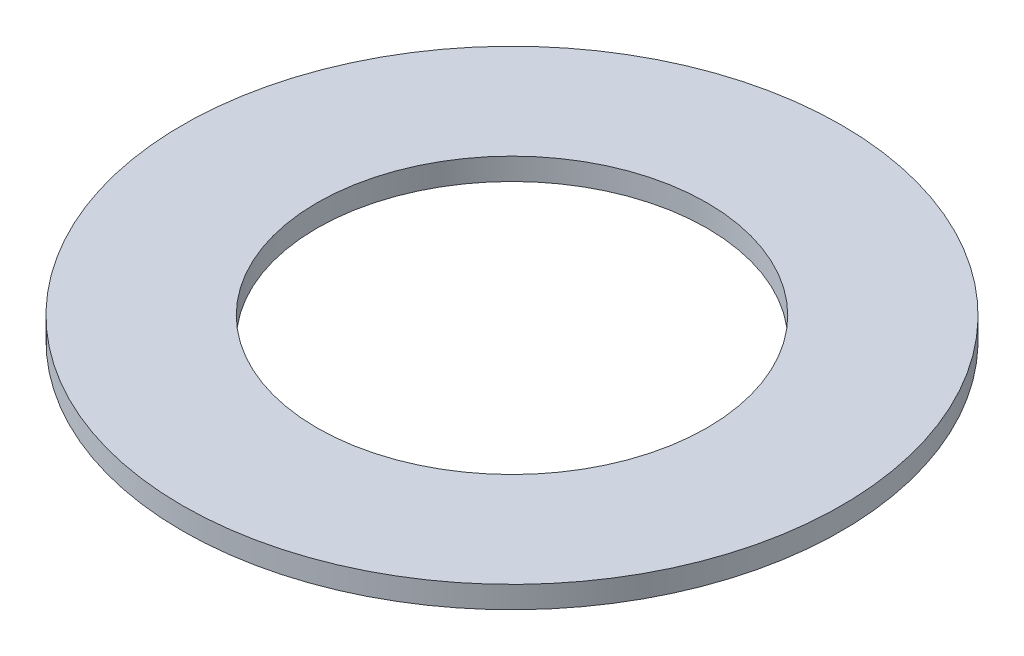
SolidWorks part; units mm, degrees
ref_plane "Front Plane" through (0, 0, 0) normal (0, 0, 1) x (1, 0, 0)
ref_plane "Top Plane" through (0, 0, 0) normal (0, 1, 0) x (1, 0, 0)
ref_plane "Right Plane" through (0, 0, 0) normal (1, 0, 0) x (0, 0, -1)
sketch "Sketch1" plane through (0, 0, 0) normal (0, 1, 0) x (1, 0, 0)
  circle A0 centre (0, 0) radius 6
  circle A1 centre (0, 0) radius 3.55
  dimension "D1" = 12
  dimension "D2" = 7.1
extrude "Boss-Extrude1" add sketch "Sketch1" along normal blind 0.4
